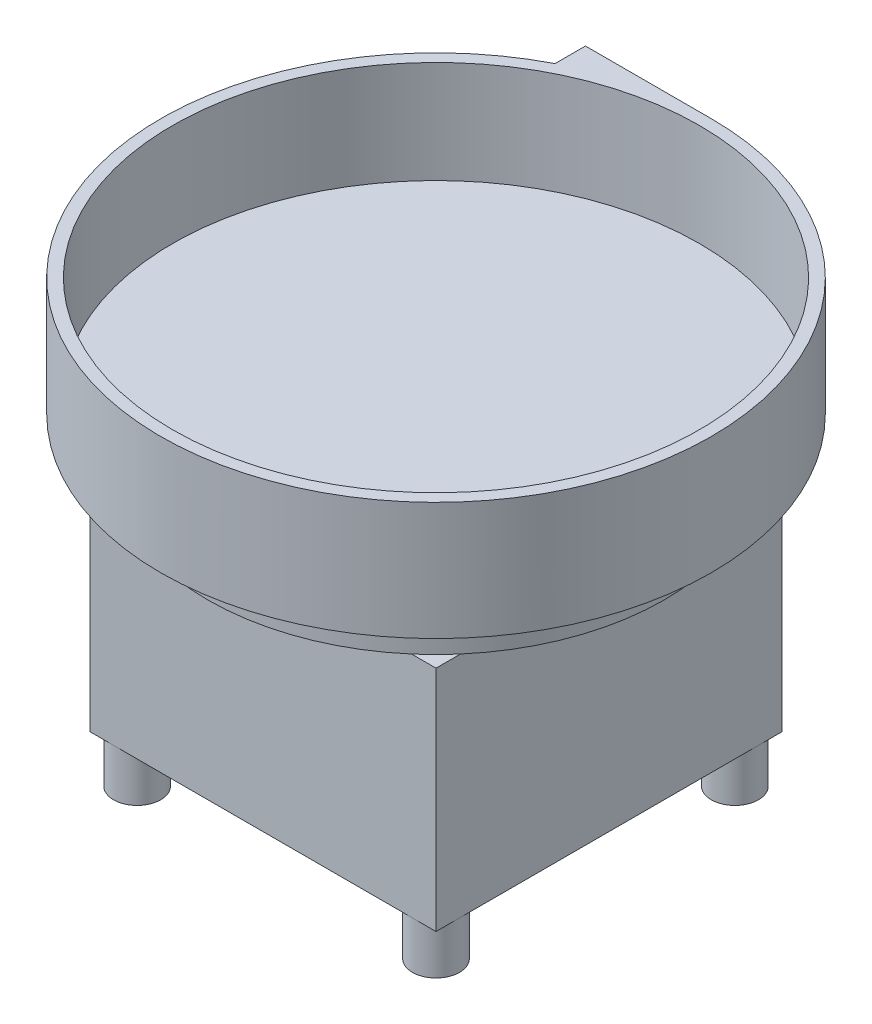
SolidWorks part; units mm, degrees
ref_plane "Front Plane" through (0, 0, 0) normal (0, 0, 1) x (1, 0, 0)
ref_plane "Top Plane" through (0, 0, 0) normal (0, 1, 0) x (1, 0, 0)
ref_plane "Right Plane" through (0, 0, 0) normal (1, 0, 0) x (0, 0, -1)
sketch "Sketch1" plane through (0, 0, 0) normal (0, 1, 0) x (1, 0, 0)
  line L1 (0, 222.25) -> (-101.6, 222.25)
  line L4 (-101.6, 222.25) -> (-101.6, 197.6677)
  arc A0 (-101.6, 197.6677) -> (0, 222.25) centre (0, 0) ccw
  circle A1 centre (0, 0) radius 212.725
  dimension "D1" = 444.5
  dimension "D3" = 425.45
  dimension "D2" = 101.6
extrude "Boss-Extrude1" add sketch "Sketch1" along normal blind 82.55
sketch "Sketch2" plane through (0, 0, 0) normal (0, -1, 0) x (1, 0, 0)
  circle A0 centre (0, 0) radius 222.25
extrude "Boss-Extrude2" add sketch "Sketch2" along normal blind 12.7
sketch "Sketch3" plane through (0, -12.7, 0) normal (0, -1, 0) x (1, 0, 0)
  circle A0 centre (0, 0) radius 184.15
  dimension "D1" = 368.3
extrude "Boss-Extrude3" add sketch "Sketch3" along normal blind 38.1
sketch "Sketch4" plane through (0, -50.8, 0) normal (0, -1, 0) x (1, 0, 0)
  line L1 (139.7, -139.7) -> (-139.7, -139.7)
  line L2 (139.7, -139.7) -> (139.7, 139.7)
  line L3 (139.7, 139.7) -> (-139.7, 139.7)
  line L4 (-139.7, -139.7) -> (-139.7, 139.7)
  line L5 (139.7, -139.7) -> (-139.7, 139.7) construction
  line L6 (139.7, 139.7) -> (-139.7, -139.7) construction
  point P0 (0, 0)
  dimension "D1" = 279.4
  dimension "D2" = 279.4
extrude "Boss-Extrude4" add sketch "Sketch4" along normal blind 184.15
sketch "Sketch5" plane through (0, -234.95, 0) normal (0, -1, 0) x (1, 0, 0)
  line L0 (-139.7, 139.7) -> (-139.7, -139.7) construction
  line L1 (-139.7, -139.7) -> (139.7, -139.7) construction
  circle A0 centre (-120.65, -120.65) radius 19.05
  circle A1 centre (-120.65, 120.65) radius 19.05
  circle A2 centre (120.65, -120.65) radius 19.05
  circle A3 centre (120.65, 120.65) radius 19.05
  dimension "D1" = 241.3
  dimension "D2" = 241.3
  dimension "D7" = 38.1
  dimension "D8" = 38.1
  dimension "D9" = 38.1
  dimension "D10" = 38.1
  dimension "D3" = 241.3
  dimension "D4" = 241.3
  dimension "D5" = 19.05
  dimension "D6" = 19.05
extrude "Boss-Extrude5" add sketch "Sketch5" along normal blind 38.1
